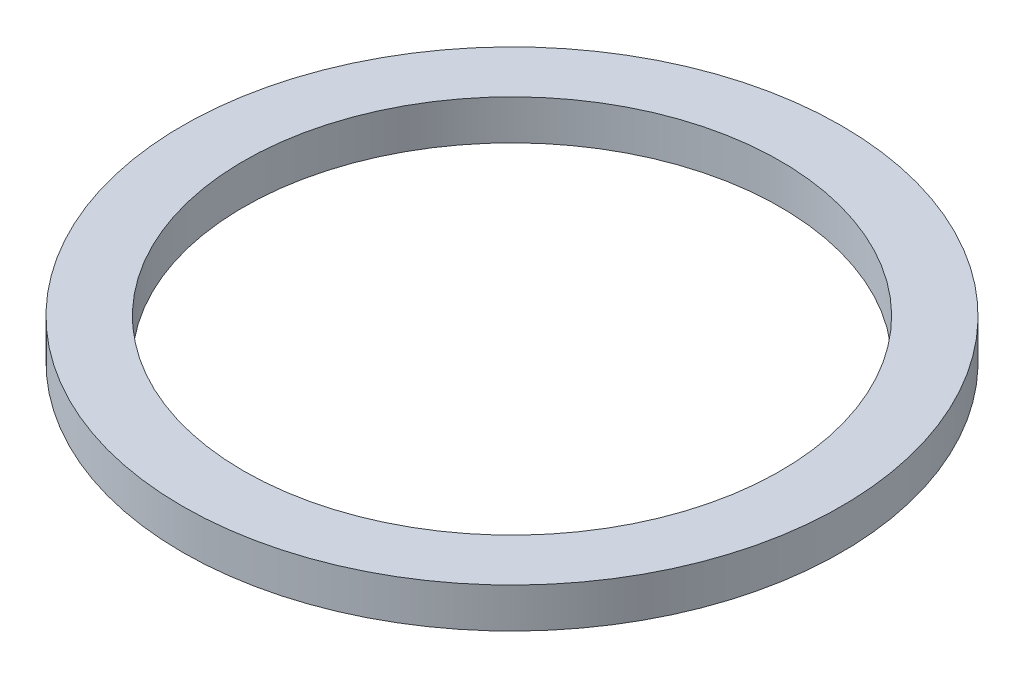
SolidWorks part; units mm, degrees
ref_plane "Front Plane" through (0, 0, 0) normal (0, 0, 1) x (1, 0, 0)
ref_plane "Top Plane" through (0, 0, 0) normal (0, 1, 0) x (1, 0, 0)
ref_plane "Right Plane" through (0, 0, 0) normal (1, 0, 0) x (0, 0, -1)
sketch "Sketch1" plane through (0, 0, 0) normal (0, 1, 0) x (1, 0, 0)
  circle A0 centre (0, 0) radius 78.74
  circle A1 centre (0, 0) radius 64.135
  dimension "D1" = 157.48
  dimension "D2" = 128.27
extrude "Boss-Extrude1" add sketch "Sketch1" along normal blind 9.525
